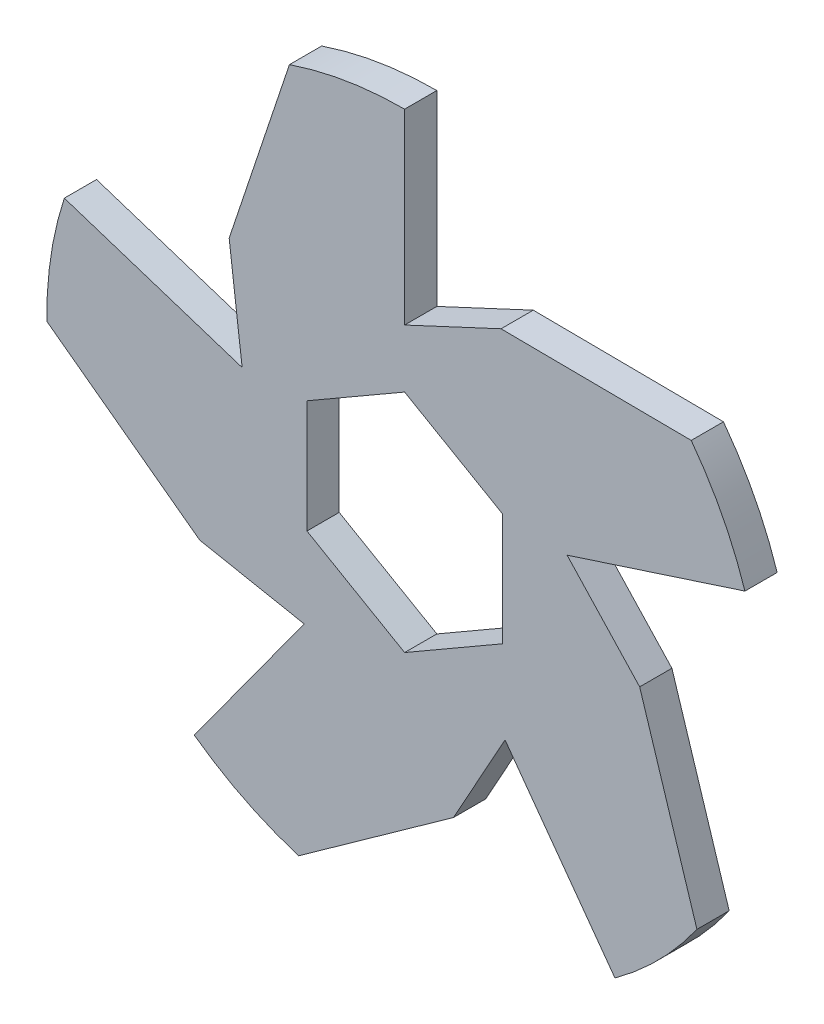
SolidWorks part; units mm, degrees
ref_plane "Frontal" through (0, 0, 0) normal (0, 0, 1) x (1, 0, 0)
ref_plane "Superior" through (0, 0, 0) normal (0, 1, 0) x (1, 0, 0)
ref_plane "Direito" through (0, 0, 0) normal (1, 0, 0) x (0, 0, -1)
sketch "Esboço1" plane through (0, 0, 0) normal (0, 0, 1) x (1, 0, 0)
  line L0 (0, 55.5) -> (0, 26.5)
  line L1 (0, 17.4937) -> (-15.15, 8.7469)
  line L2 (-15.15, 8.7469) -> (-15.15, -8.7469)
  line L3 (-15.15, -8.7469) -> (0, -17.4937)
  line L4 (0, -17.4937) -> (15.15, -8.7469)
  line L5 (15.15, -8.7469) -> (15.15, 8.7469)
  line L6 (15.15, 8.7469) -> (0, 17.4937)
  line L7 (0, 26.5) -> (14.9541, 33.4732)
  line L8 (14.9541, 33.4732) -> (44.4531, 33.2291)
  line L9 (36.456, -3.8784) -> (45.3395, -32.009)
  line L10 (25.203, 8.189) -> (36.456, -3.8784)
  line L11 (52.7836, 17.1504) -> (25.203, 8.189)
  line L12 (7.577, -35.8702) -> (-16.4317, -53.0118)
  line L13 (15.5763, -21.439) -> (7.577, -35.8702)
  line L14 (32.6221, -44.9004) -> (15.5763, -21.439)
  line L15 (-31.7732, -18.2906) -> (-55.4949, -0.7541)
  line L16 (-15.5763, -21.439) -> (-31.7732, -18.2906)
  line L17 (-32.6221, -44.9004) -> (-15.5763, -21.439)
  line L18 (-27.2138, 24.566) -> (-17.866, 52.5457)
  line L19 (-25.203, 8.189) -> (-27.2138, 24.566)
  line L20 (-52.7836, 17.1504) -> (-25.203, 8.189)
  circle A0 centre (0, 0) radius 15.15 construction
  circle A1 centre (0, 0) radius 55.5
  circle A2 centre (0, 0) radius 55.5
  circle A3 centre (0, 0) radius 55.5
  circle A4 centre (0, 0) radius 55.5
  circle A5 centre (0, 0) radius 55.5
  point P36 (0, 0)
  dimension "D2" = 111
  dimension "D1" = 30.3
  dimension "D3" = 65
  dimension "D4" = 29
  dimension "D5" = 16.5
  dimension "D6" = 29.5
  dimension "D7" = 5
extrude "Ressalto-extrusão1" add sketch "Esboço1" along normal blind 5 contours L11 A1 L8 L7 L0 L18 L19 L20 L15 L16 L17 L12 L13 L14 L9 L10 L6 L5 L4 L3 L2 L1
